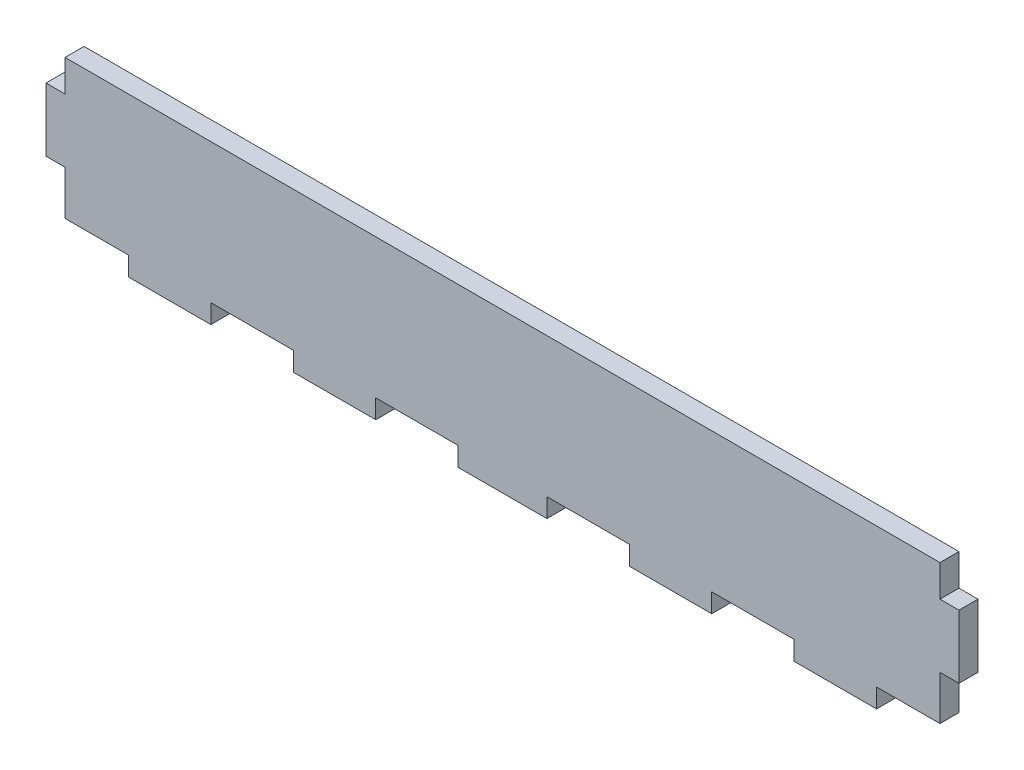
SolidWorks part; units mm, degrees
ref_plane "Front Plane" through (0, 0, 0) normal (0, 0, 1) x (1, 0, 0)
ref_plane "Top Plane" through (0, 0, 0) normal (0, 1, 0) x (1, 0, 0)
ref_plane "Right Plane" through (0, 0, 0) normal (1, 0, 0) x (0, 0, -1)
sketch "Sketch1" plane through (0, 0, 0) normal (0, 0, 1) x (1, 0, 0)
  line L0 (0, 17) -> (0, 22)
  line L1 (0, 0) -> (10, 0)
  line L2 (0, 0) -> (0, 7)
  line L3 (0, 22) -> (138, 22)
  line L4 (138, 0) -> (138, 7)
  line L5 (0, 17) -> (-3, 17)
  line L6 (138, 17) -> (138, 22)
  line L7 (0, 7) -> (-3, 7)
  line L8 (-3, 17) -> (-3, 7)
  line L9 (138, 17) -> (141, 17)
  line L10 (23, 0) -> (36, 0)
  line L11 (138, 7) -> (141, 7)
  line L12 (141, 17) -> (141, 7)
  line L14 (10, 0) -> (10, -3)
  line L15 (10, -3) -> (23, -3)
  line L16 (23, 0) -> (23, -3)
  line L18 (36, 0) -> (36, -3)
  line L19 (36, -3) -> (49, -3)
  line L20 (49, 0) -> (49, -3)
  line L22 (62, 0) -> (62, -3)
  line L23 (62, -3) -> (76, -3)
  line L24 (76, 0) -> (76, -3)
  line L26 (89, 0) -> (89, -3)
  line L27 (89, -3) -> (102, -3)
  line L28 (102, 0) -> (102, -3)
  line L30 (115, 0) -> (115, -3)
  line L31 (115, -3) -> (128, -3)
  line L32 (128, 0) -> (128, -3)
  line L33 (49, 0) -> (62, 0)
  line L34 (76, 0) -> (89, 0)
  line L35 (102, 0) -> (115, 0)
  line L36 (128, 0) -> (138, 0)
  dimension "D1" = 138
  dimension "D2" = 22
  dimension "D3" = 5
  dimension "D4" = 7
  dimension "D5" = 3
  dimension "D6" = 14
  dimension "D7" = 10
  dimension "D8" = 10
  dimension "D9" = 13
  dimension "D10" = 13
  dimension "D11" = 13
  dimension "D12" = 13
  dimension "D13" = 13
  dimension "D14" = 13
  dimension "D15" = 13
  dimension "D16" = 3
extrude "Boss-Extrude1" add sketch "Sketch1" along normal blind 3
